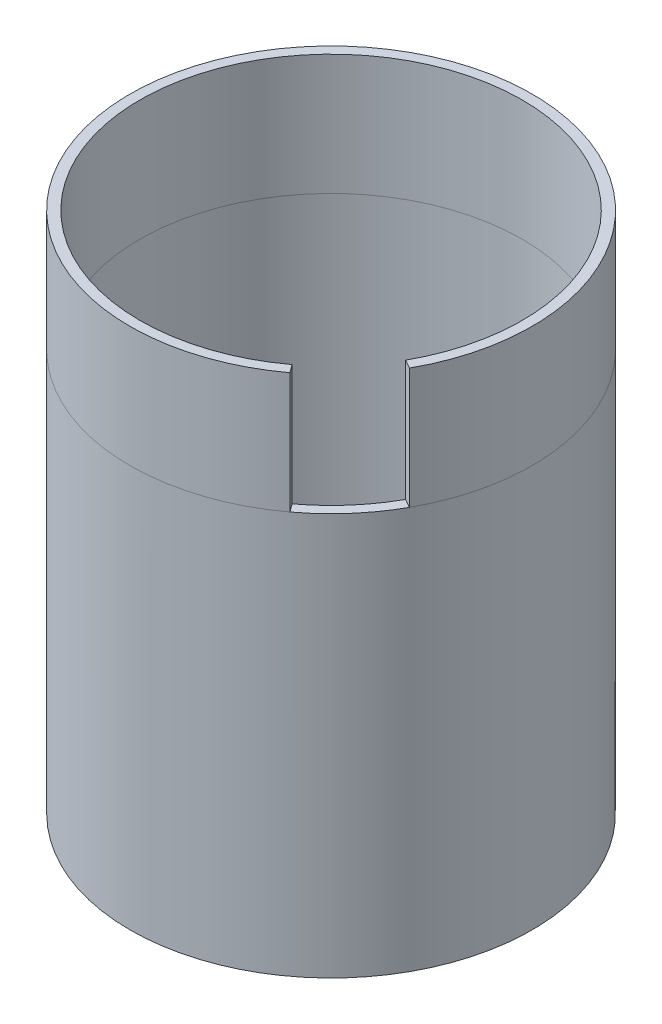
SolidWorks part; units mm, degrees
ref_plane "前基準面" through (0, 0, 0) normal (0, 0, 1) x (1, 0, 0)
ref_plane "上基準面" through (0, 0, 0) normal (0, 1, 0) x (1, 0, 0)
ref_plane "右基準面" through (0, 0, 0) normal (1, 0, 0) x (0, 0, -1)
sketch "草圖1" plane through (0, 0, 0) normal (0, 1, 0) x (1, 0, 0)
  circle A0 centre (0, 0) radius 4.75
  circle A1 centre (0, 0) radius 5
  dimension "D1" = 9.5
  dimension "D2" = 10
extrude "填料-伸長3" add sketch "草圖1" along normal blind 10
sketch "草圖2" plane through (0, 10, 0) normal (0, 1, 0) x (1, 0, 0)
  line L0 (-0.0018, 0.0015) -> (2.8382, -3.8088) construction
  line L1 (2.8382, -3.8088) -> (2.9876, -4.0092)
  line L2 (-0.0018, 0.0015) -> (4.1544, -2.3029) construction
  line L3 (4.1544, -2.3029) -> (4.373, -2.4241)
  arc A1 (2.8382, -3.8088) -> (4.1544, -2.3029) centre (-0.0018, 0.0015) cw
  circle A2 centre (0, 0) radius 4.75 construction
  arc A3 (4.373, -2.4241) -> (2.9876, -4.0092) centre (-0.0018, 0.0015) ccw
  circle A4 centre (0, 0) radius 5 construction
  dimension "D1" = 2
extrude "填料-伸長5" add sketch "草圖2" along normal blind 3
